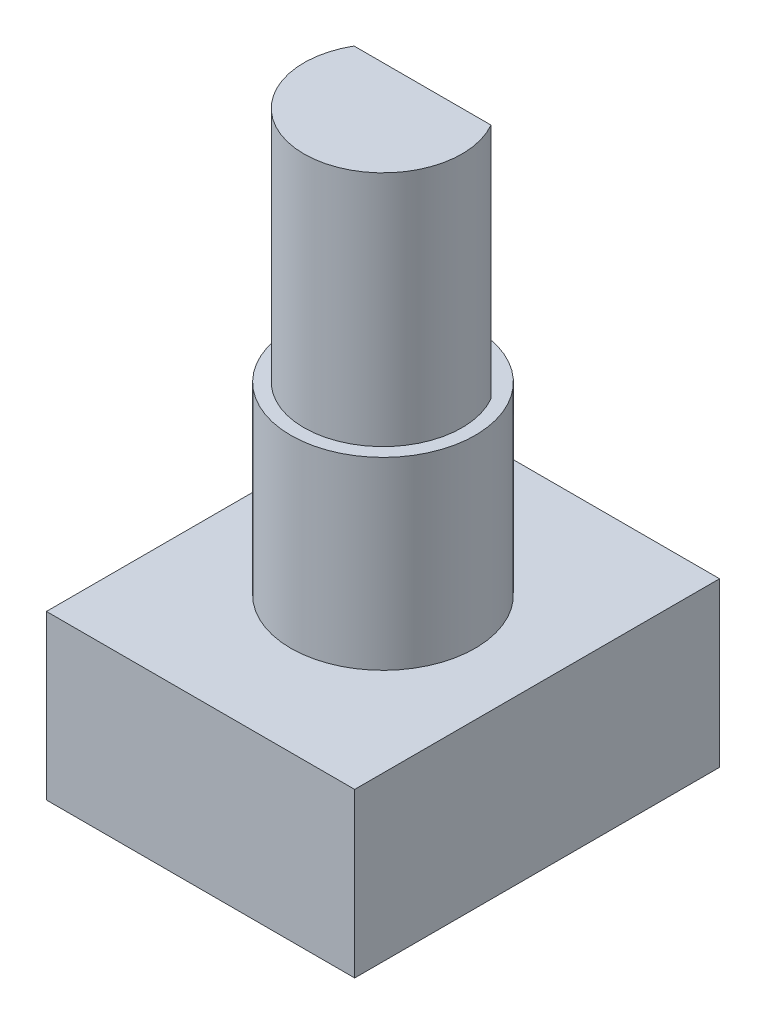
SolidWorks part; units mm, degrees
ref_plane "Front Plane" through (0, 0, 0) normal (0, 0, 1) x (1, 0, 0)
ref_plane "Top Plane" through (0, 0, 0) normal (0, 1, 0) x (1, 0, 0)
ref_plane "Right Plane" through (0, 0, 0) normal (1, 0, 0) x (0, 0, -1)
sketch "Sketch1" plane through (0, 0, 0) normal (0, 1, 0) x (1, 0, 0)
  line L1 (0, 0) -> (11.7, 0)
  line L2 (0, 0) -> (0, 13.85)
  line L3 (0, 13.85) -> (11.7, 13.85)
  line L4 (11.7, 0) -> (11.7, 13.85)
  dimension "D1" = 11.7
  dimension "D2" = 13.85
extrude "Boss-Extrude1" add sketch "Sketch1" along normal blind 6.2
sketch "Sketch2" plane through (0, 6.2, 0) normal (0, 1, 0) x (1, 0, 0)
  line L0 (0, 13.85) -> (11.7, 0) construction
  circle A0 centre (5.85, 6.925) radius 3.5
  dimension "D1" = 7
extrude "Boss-Extrude2" add sketch "Sketch2" along normal blind 7
sketch "Sketch3" plane through (0, 13.2, 0) normal (0, 1, 0) x (1, 0, 0)
  line L0 (3.2519, 8.425) -> (8.4481, 8.425)
  arc A0 (3.2519, 8.425) -> (8.4481, 8.425) centre (5.85, 6.925) ccw
  dimension "D1" = 6
  dimension "D2" = 1.5
extrude "Boss-Extrude3" add sketch "Sketch3" along normal blind 9
